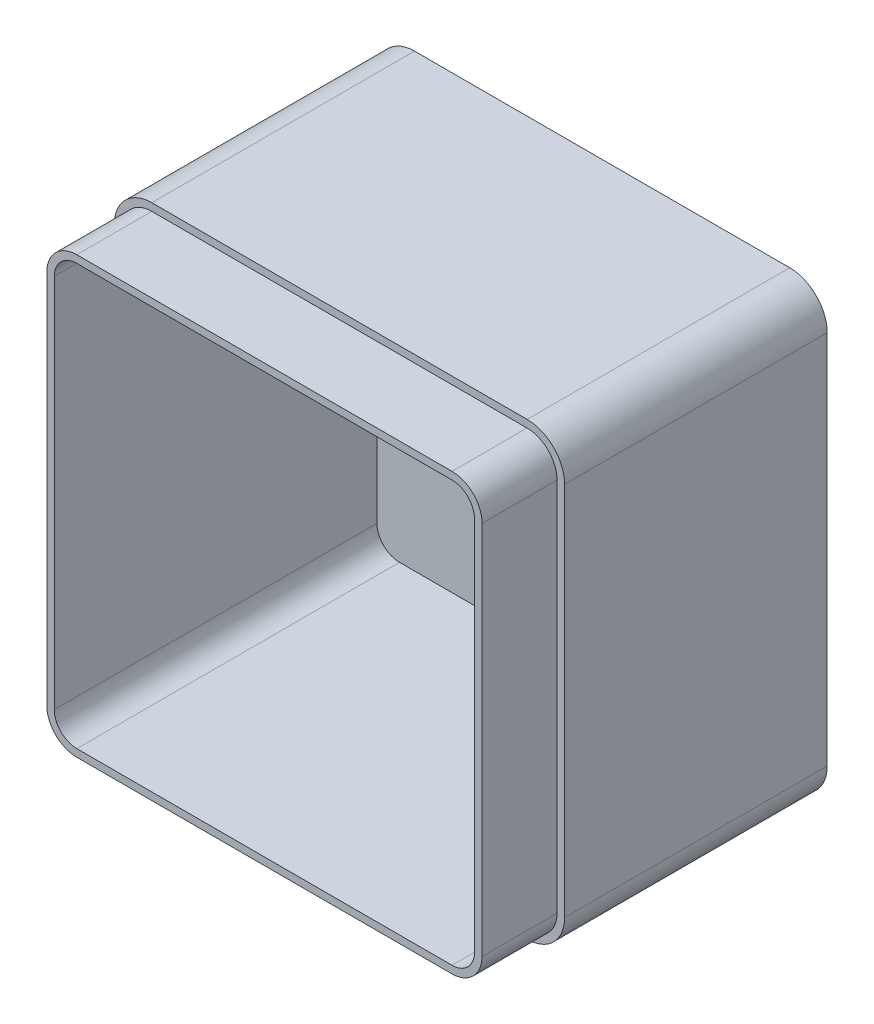
SolidWorks part; units mm, degrees
ref_plane "Front Plane" through (0, 0, 0) normal (0, 0, 1) x (1, 0, 0)
ref_plane "Top Plane" through (0, 0, 0) normal (0, 1, 0) x (1, 0, 0)
ref_plane "Right Plane" through (0, 0, 0) normal (1, 0, 0) x (0, 0, -1)
sketch "Sketch1" plane through (0, 0, 0) normal (0, 0, 1) x (1, 0, 0)
  line L1 (0, 0) -> (120, 0)
  line L2 (0, 0) -> (0, 120)
  line L3 (0, 120) -> (120, 120)
  line L4 (120, 0) -> (120, 120)
  dimension "D1" = 120
  dimension "D2" = 120
extrude "Boss-Extrude1" add sketch "Sketch1" along normal blind 90
fillet "Fillet1" radius 10 4 edges at (0, 0, 45) (120, 0, 45) (0, 120, 45) (120, 120, 45)
shell "Shell1" thickness 4
sketch "Sketch3" plane through (0, 0, 90) normal (0, 0, 1) x (1, 0, 0)
  line L4 (0, 110) -> (0, 10)
  line L5 (10, 0) -> (110, 0)
  line L6 (120, 10) -> (120, 110)
  line L7 (110, 120) -> (10, 120)
  line L8 (0, 110) -> (0, 10)
  line L9 (10, 0) -> (110, 0)
  line L10 (120, 10) -> (120, 110)
  line L11 (110, 120) -> (10, 120)
  line L16 (2, 110) -> (2, 10)
  line L17 (10, 2) -> (110, 2)
  line L18 (118, 10) -> (118, 110)
  line L19 (110, 118) -> (10, 118)
  line L20 (2, 110) -> (2, 10)
  line L21 (10, 2) -> (110, 2)
  line L22 (118, 10) -> (118, 110)
  line L23 (110, 118) -> (10, 118)
  arc A4 (0, 10) -> (10, 0) centre (10, 10) ccw
  arc A5 (110, 0) -> (120, 10) centre (110, 10) ccw
  arc A6 (120, 110) -> (110, 120) centre (110, 110) ccw
  arc A7 (10, 120) -> (0, 110) centre (10, 110) ccw
  arc A8 (0, 10) -> (10, 0) centre (10, 10) ccw
  arc A9 (110, 0) -> (120, 10) centre (110, 10) ccw
  arc A10 (120, 110) -> (110, 120) centre (110, 110) ccw
  arc A11 (10, 120) -> (0, 110) centre (10, 110) ccw
  arc A16 (2, 10) -> (10, 2) centre (10, 10) ccw
  arc A17 (110, 2) -> (118, 10) centre (110, 10) ccw
  arc A18 (118, 110) -> (110, 118) centre (110, 110) ccw
  arc A19 (10, 118) -> (2, 110) centre (10, 110) ccw
  arc A20 (2, 10) -> (10, 2) centre (10, 10) ccw
  arc A21 (110, 2) -> (118, 10) centre (110, 10) ccw
  arc A22 (118, 110) -> (110, 118) centre (110, 110) ccw
  arc A23 (10, 118) -> (2, 110) centre (10, 110) ccw
  dimension "D1" = 0
  dimension "D2" = 2
extrude "Cut-Extrude1" cut sketch "Sketch3" against normal blind 20
